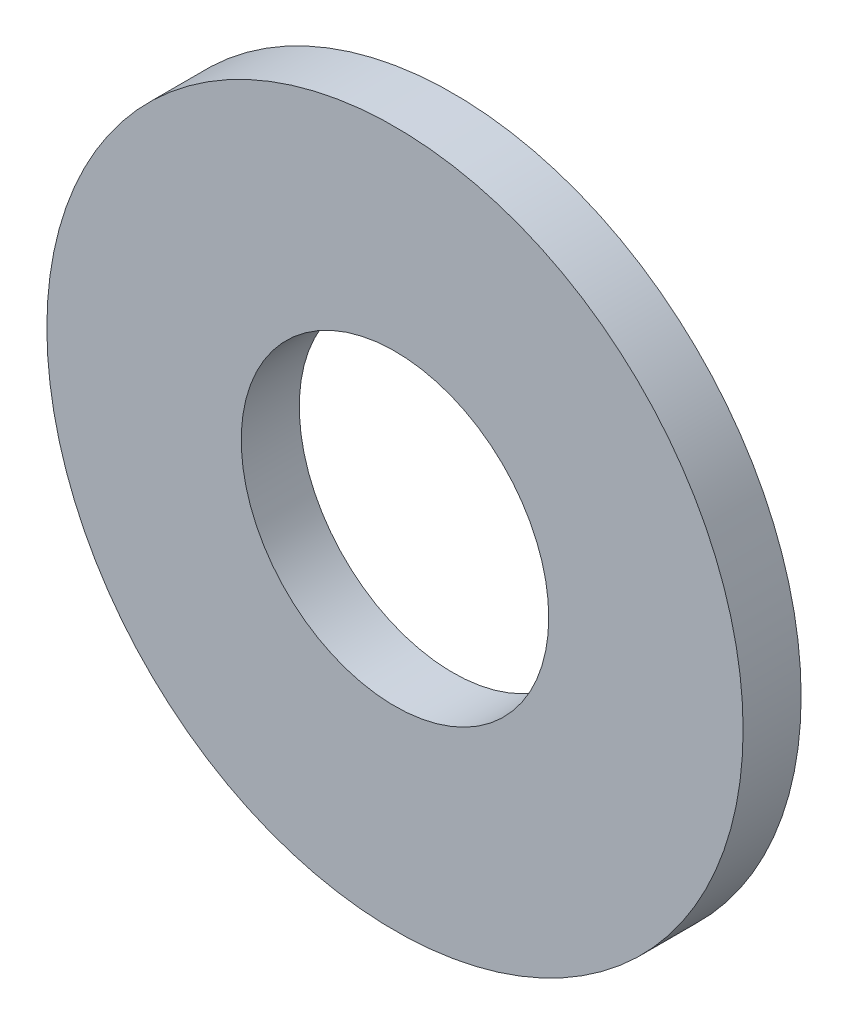
SolidWorks part; units mm, degrees
material "Laiton"
ref_plane "Plan de face" through (0, 0, 0) normal (0, 0, 1) x (1, 0, 0)
ref_plane "Plan de dessus" through (0, 0, 0) normal (0, 1, 0) x (1, 0, 0)
ref_plane "Plan de droite" through (0, 0, 0) normal (1, 0, 0) x (0, 0, -1)
sketch "Esquisse1" plane through (0, 0, 0) normal (0, 0, 1) x (1, 0, 0)
  circle A0 centre (0, 0) radius 2.65
  circle A1 centre (0, 0) radius 6
  dimension "D1" = 12
  dimension "D2" = 5.3
extrude "Extrusion1" add sketch "Esquisse1" along normal blind 1
